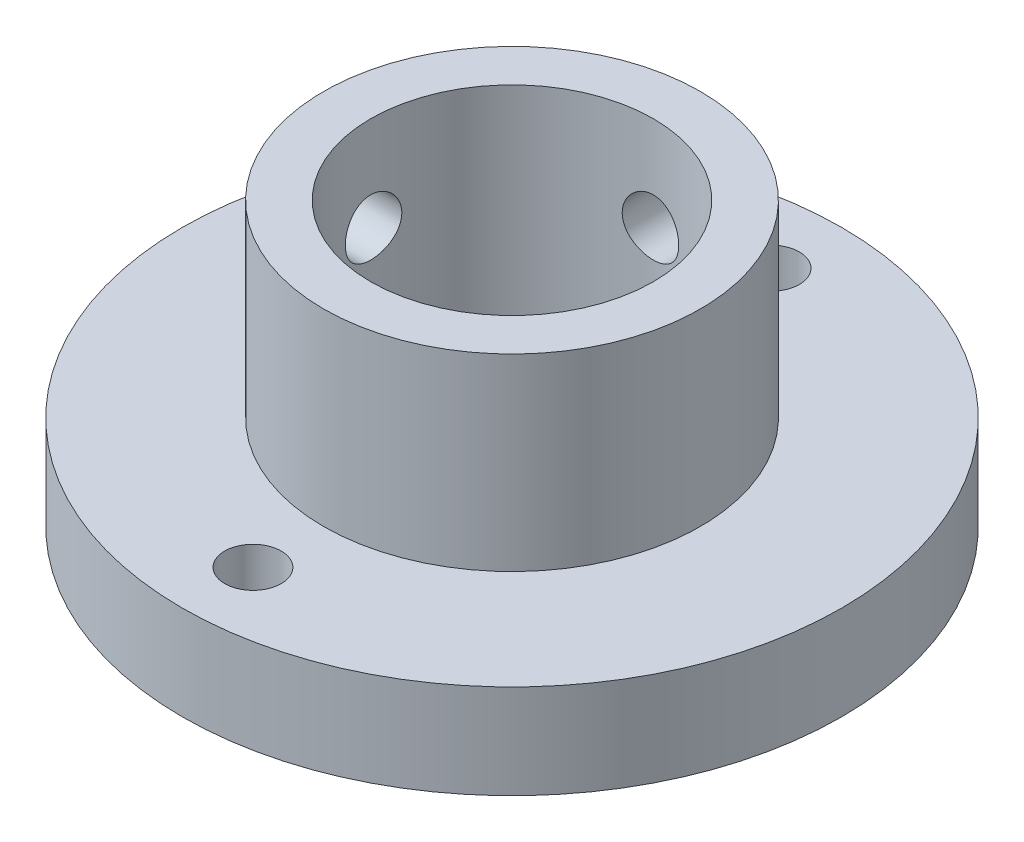
SolidWorks part; units mm, degrees
material "Náilon 101"
ref_plane "Plano frontal" through (0, 0, 0) normal (0, 0, 1) x (1, 0, 0)
ref_plane "Plano superior" through (0, 0, 0) normal (0, 1, 0) x (1, 0, 0)
ref_plane "Plano direito" through (0, 0, 0) normal (1, 0, 0) x (0, 0, -1)
sketch "Esboço1" plane through (0, 0, 0) normal (0, 1, 0) x (1, 0, 0)
  circle A0 centre (0, 0) radius 17.5
  dimension "D1" = 35
extrude "Ressalto-extrusão1" add sketch "Esboço1" along normal blind 5
sketch "Esboço2" plane through (0, 5, 0) normal (0, 1, 0) x (1, 0, 0)
  circle A0 centre (0, 0) radius 10
  dimension "D1" = 20
extrude "Ressalto-extrusão2" add sketch "Esboço2" along normal blind 10
sketch "Esboço3" plane through (0, 15, 0) normal (0, 1, 0) x (1, 0, 0)
  circle A0 centre (0, 0) radius 7.5
  dimension "D1" = 15
extrude "Corte-extrusão1" cut sketch "Esboço3" against normal through all
sketch "Esboço4" plane through (0, 5, 0) normal (0, 1, 0) x (1, 0, 0)
  line L0 (0, 10) -> (0, 17.5) construction
  circle A0 centre (0, 0) radius 10 construction
  circle A1 centre (0, 0) radius 10 construction
  circle A2 centre (0, 0) radius 17.5 construction
  circle A3 centre (0, 13.75) radius 1.5
  circle A4 centre (0, -13.75) radius 1.5
  point P15 (0, 0.375)
  point P16 (0, 0)
  point P20 (0, 0)
  dimension "D1" = 3
  dimension "D2" = 2
extrude "Corte-extrusão2" cut sketch "Esboço4" against normal blind 10
sketch "Esboço5" plane through (0, 0, 0) normal (0, 0, 1) x (1, 0, 0)
  line L0 (0, 15) -> (0, 5) construction
  line L1 (10, 15) -> (-10, 15) construction
  line L2 (17.5, 5) -> (-17.5, 5) construction
  circle A0 centre (0, 10) radius 1.5
  dimension "D1" = 3
extrude "Corte-extrusão3" cut sketch "Esboço5" against normal blind 10
sketch "Esboço6" plane through (0, 0, 0) normal (1, 0, 0) x (0, 0, -1)
  line L0 (0, 5) -> (0, 15) construction
  line L1 (17.5, 5) -> (-17.5, 5) construction
  line L2 (7.5, 15) -> (-7.5, 15) construction
  circle A0 centre (0, 10) radius 1.5
  dimension "D1" = 3
extrude "Corte-extrusão4" cut sketch "Esboço6" against normal blind 10
